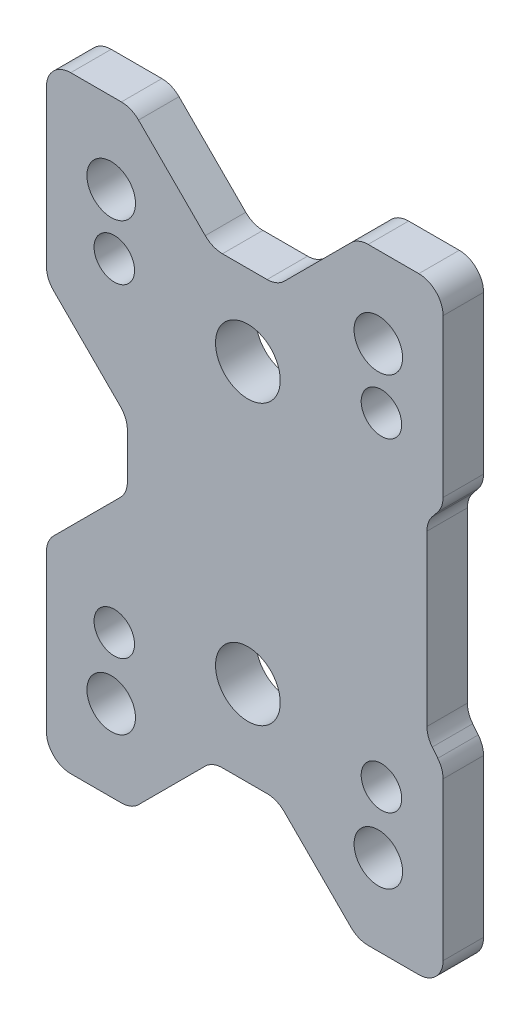
SolidWorks part; units mm, degrees
ref_plane "Front Plane" through (0, 0, 0) normal (0, 0, 1) x (1, 0, 0)
ref_plane "Top Plane" through (0, 0, 0) normal (0, 1, 0) x (1, 0, 0)
ref_plane "Right Plane" through (0, 0, 0) normal (1, 0, 0) x (0, 0, -1)
sketch "Sketch2" plane through (0, 0, 0) normal (0, 0, 1) x (1, 0, 0)
  line L0 (-15.6262, 37.2123) -> (-21.8836, 37.2123)
  line L1 (-24.8836, 34.2123) -> (-24.8836, 14.9549)
  line L2 (-24.0049, 12.8336) -> (-15.7623, 4.591)
  line L3 (-14.8836, 2.4697) -> (-14.8836, -3.0451)
  line L4 (-15.7623, -5.1664) -> (-24.0049, -13.409)
  line L5 (-24.8836, -15.5303) -> (-24.8836, -34.7877)
  line L6 (-21.8836, -37.7877) -> (-15.6262, -37.7877)
  line L7 (-13.5049, -36.909) -> (-5.2623, -28.6664)
  line L8 (-3.1409, -27.7877) -> (2.3738, -27.7877)
  line L9 (4.4951, -28.6664) -> (12.7377, -36.909)
  line L10 (14.8591, -37.7877) -> (21.1164, -37.7877)
  line L11 (24.1164, -34.7877) -> (24.1164, -15.34)
  line L12 (23.459, -13.466) -> (22.7738, -12.6094)
  line L13 (22.1164, -10.7353) -> (22.1164, 10.16)
  line L14 (22.7738, 12.034) -> (23.459, 12.8906)
  line L15 (24.1164, 14.7647) -> (24.1164, 34.2123)
  line L16 (21.1164, 37.2123) -> (14.8591, 37.2123)
  line L17 (12.7377, 36.3336) -> (4.4951, 28.091)
  line L18 (2.3738, 27.2123) -> (-3.1409, 27.2123)
  line L19 (-5.2623, 28.091) -> (-13.5049, 36.3336)
  circle A0 centre (-16.8836, -27.7877) radius 3
  circle A1 centre (16.1164, -27.7877) radius 3
  circle A2 centre (16.1164, 27.2123) radius 3
  circle A3 centre (-16.8836, 27.2123) radius 3
  arc A4 (-21.8836, 37.2123) -> (-24.8836, 34.2123) centre (-21.8836, 34.2123) ccw
  arc A5 (-24.8836, 14.9549) -> (-24.0049, 12.8336) centre (-21.8836, 14.9549) ccw
  arc A6 (-14.8836, 2.4697) -> (-15.7623, 4.591) centre (-17.8836, 2.4697) ccw
  arc A7 (-15.7623, -5.1664) -> (-14.8836, -3.0451) centre (-17.8836, -3.0451) ccw
  arc A8 (-24.0049, -13.409) -> (-24.8836, -15.5303) centre (-21.8836, -15.5303) ccw
  arc A9 (-24.8836, -34.7877) -> (-21.8836, -37.7877) centre (-21.8836, -34.7877) ccw
  arc A10 (-15.6262, -37.7877) -> (-13.5049, -36.909) centre (-15.6262, -34.7877) ccw
  arc A11 (-3.1409, -27.7877) -> (-5.2623, -28.6664) centre (-3.1409, -30.7877) ccw
  arc A12 (4.4951, -28.6664) -> (2.3738, -27.7877) centre (2.3738, -30.7877) ccw
  arc A13 (12.7377, -36.909) -> (14.8591, -37.7877) centre (14.8591, -34.7877) ccw
  arc A14 (21.1164, -37.7877) -> (24.1164, -34.7877) centre (21.1164, -34.7877) ccw
  arc A15 (24.1164, -15.34) -> (23.459, -13.466) centre (21.1164, -15.34) ccw
  arc A16 (22.1164, -10.7353) -> (22.7738, -12.6094) centre (25.1164, -10.7353) ccw
  arc A17 (22.7738, 12.034) -> (22.1164, 10.16) centre (25.1164, 10.16) ccw
  arc A18 (23.459, 12.8906) -> (24.1164, 14.7647) centre (21.1164, 14.7647) ccw
  arc A19 (24.1164, 34.2123) -> (21.1164, 37.2123) centre (21.1164, 34.2123) ccw
  arc A20 (14.8591, 37.2123) -> (12.7377, 36.3336) centre (14.8591, 34.2123) ccw
  arc A21 (2.3738, 27.2123) -> (4.4951, 28.091) centre (2.3738, 30.2123) ccw
  arc A22 (-5.2623, 28.091) -> (-3.1409, 27.2123) centre (-3.1409, 30.2123) ccw
  arc A23 (-13.5049, 36.3336) -> (-15.6262, 37.2123) centre (-15.6262, 34.2123) ccw
  dimension "D1" = 6
  dimension "D2" = 6
  dimension "D3" = 6
  dimension "D4" = 6
  dimension "D5" = 49
  dimension "D6" = 75
extrude "Boss-Extrude1" add sketch "Sketch2" along normal blind 5
sketch "Sketch7" plane through (0, 0, 0) normal (0, 0, -1) x (-1, 0, 0)
  line L0 (-24.1164, 24.4885) -> (-42.0953, 24.4885) construction
  line L1 (-24.1164, 14.7647) -> (-24.1164, 34.2123) construction
  line L3 (-24.1164, 34.4885) -> (-29.1164, 34.4885)
  line L4 (-24.1164, 34.4885) -> (-24.1164, 14.4885)
  line L5 (-24.1164, 14.4885) -> (-29.1164, 14.4885)
  line L6 (-34.1164, 29.4885) -> (-34.1164, 19.4885)
  arc A0 (-29.1164, 14.4885) -> (-34.1164, 19.4885) centre (-29.1164, 19.4885) cw
  arc A1 (-34.1164, 29.4885) -> (-29.1164, 34.4885) centre (-29.1164, 29.4885) cw
  point P10 (-34.1164, 14.4885)
  point P13 (-34.1164, 34.4885)
  line M33 (-24.1164, 34.2123) -> (-24.1164, 14.7647)
  dimension "D4" = 5
  dimension "D1" = 10
  dimension "D2" = 20
  dimension "D3" = 10
extrude "Boss-Extrude3" add sketch "Sketch7" against normal through all contours L0 L3 A1 L6 M33 | L4 L0 L6 A0 L5
sketch "Sketch9" plane through (0, 0, 0) normal (0, 0, -1) x (-1, 0, 0)
  line L0 (-24.1164, 34.4885) -> (-24.1164, 14.4885)
  line L1 (-24.1164, 14.4885) -> (-29.1164, 14.4885) construction
  line L2 (-34.1164, 29.4885) -> (-34.1164, 19.4885) construction
  line L3 (-24.1164, 34.4885) -> (-29.1164, 34.4885) construction
  line L4 (-24.1164, 14.4885) -> (-29.1164, 14.4885)
  line L5 (-34.1164, 29.4885) -> (-34.1164, 19.4885)
  line L6 (-24.1164, 34.4885) -> (-29.1164, 34.4885)
  arc A0 (-34.1164, 19.4885) -> (-29.1164, 14.4885) centre (-29.1164, 19.4885) ccw construction
  arc A1 (-29.1164, 34.4885) -> (-34.1164, 29.4885) centre (-29.1164, 29.4885) ccw construction
  arc A2 (-34.1164, 19.4885) -> (-29.1164, 14.4885) centre (-29.1164, 19.4885) ccw
  arc A3 (-29.1164, 34.4885) -> (-34.1164, 29.4885) centre (-29.1164, 29.4885) ccw
extrude "Cut-Extrude5" cut sketch "Sketch9" against normal through all
sketch "Sketch10" plane through (0, 0, 5) normal (0, 0, 1) x (1, 0, 0)
  line L0 (-39.5478, 0) -> (30.9586, 0) construction
  line L1 (0, 36.9693) -> (0, -32.7708) construction
  line L2 (16.5, 20.8471) -> (16.5, -54.5274) construction
  line L3 (-16.5, 20.8471) -> (-16.5, -54.5274) construction
  circle A0 centre (0, 17.25) radius 4
  circle A1 centre (0, -17.25) radius 4
  circle A2 centre (16.5, 20) radius 2.5
  circle A3 centre (16.5, -20) radius 2.5
  circle A4 centre (-16.5, -20) radius 2.5
  circle A5 centre (-16.5, 20) radius 2.5
  point P15 (0, 0)
  point P16 (0, 0)
  point P17 (0, 0)
  point P18 (0, 0)
  point P19 (0, 0)
  point P20 (0, 0)
  point P21 (0, 0)
  point P22 (0, 0)
  point P29 (0, 0)
  dimension "D1" = 8
  dimension "D2" = 8
  dimension "D3" = 34.5
  dimension "D4" = 5
  dimension "D5" = 5
  dimension "D6" = 40
  dimension "D7" = 16.5
other "AlignGroup1"
extrude "Cut-Extrude6" cut sketch "Sketch10" against normal blind 10
